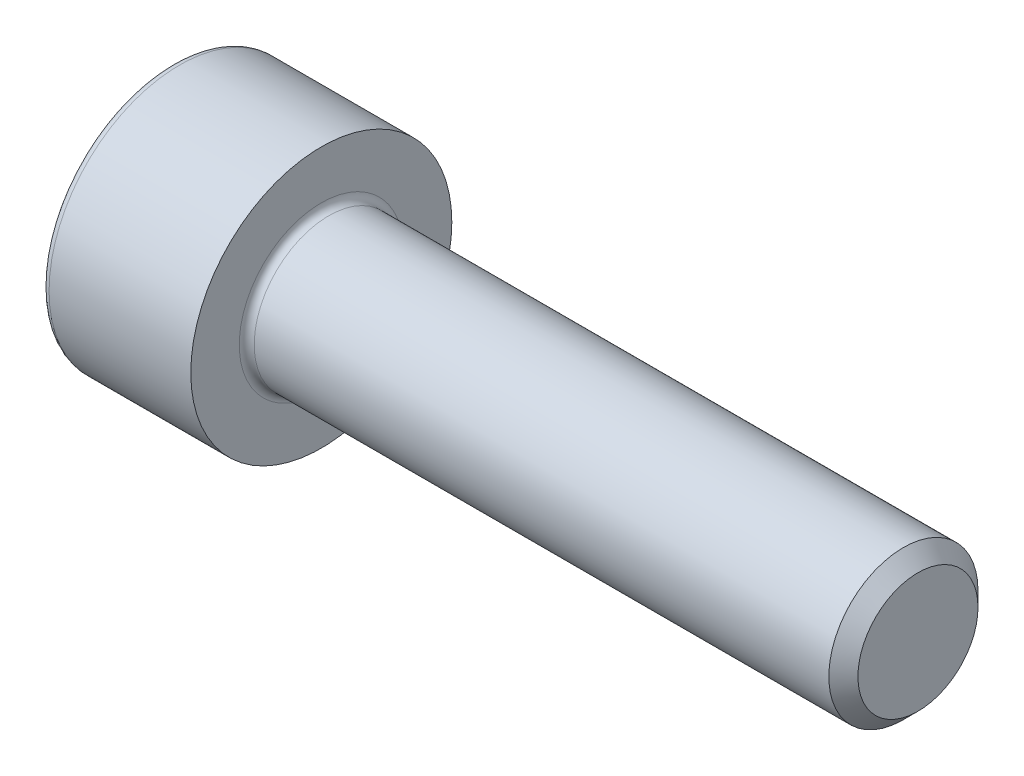
SolidWorks part; units mm, degrees
material "AISI 4340 Aço recozido"
ref_plane "Plano frontal" through (0, 0, 0) normal (0, 0, 1) x (1, 0, 0)
ref_plane "Plano superior" through (0, 0, 0) normal (0, 1, 0) x (1, 0, 0)
ref_plane "Plano direito" through (0, 0, 0) normal (1, 0, 0) x (0, 0, -1)
ref_plane "Plano1" through (0, 0, 0) normal (0, 0, -1) x (-1, 0, 0)
sketch "Esboço1" plane through (0, 0, 0) normal (0, 0, -1) x (-1, 0, 0)
  line L0 (-4, 3.5) -> (-4, 0)
  line L1 (-4, 0) -> (0, 0)
  line L2 (0, 0) -> (0, 3.5)
  line L3 (0, 3.5) -> (-4, 3.5)
  line L4 (-4, 0) -> (0, 0) construction
revolve "Revolução1" add sketch "Esboço1" angle 360 about L4
sketch "Esboço2" plane through (4, 0, 0) normal (1, 0, 0) x (0, 0, -1)
  circle A0 centre (0, 0) radius 2
extrude "Ressalto-extrusão1" add sketch "Esboço2" along normal blind 16
sketch "Esboço3" plane through (0, 0, 0) normal (-1, 0, 0) x (0, 0, 1)
  line L0 (0, -1.773) -> (1.5355, -0.8865)
  line L1 (1.5355, -0.8865) -> (1.5355, 0.8865)
  line L2 (1.5355, 0.8865) -> (0, 1.773)
  line L3 (0, 1.773) -> (-1.5355, 0.8865)
  line L4 (-1.5355, 0.8865) -> (-1.5355, -0.8865)
  line L5 (-1.5355, -0.8865) -> (0, -1.773)
extrude "Corte-extrusão1" cut sketch "Esboço3" against normal blind 2
sketch "Esboço4" plane through (0, 0, 0) normal (0, 0, 1) x (1, 0, 0)
  line L0 (2, 1.5355) -> (2, 0)
  line L1 (2, 0) -> (2.8865, 0)
  line L2 (2.8865, 0) -> (2, 1.5355)
  line L3 (2, 0) -> (2.8865, 0) construction
revolve "Corte-Revolução1" cut sketch "Esboço4" angle 360 about L3
chamfer "Chanfro1" distance 0.39 angle 45 1 edges at (20, 0, -2)
fillet "Filete1" radius 0.2 2 edges at (0, 0, 3.5) (4, 0, -2)
